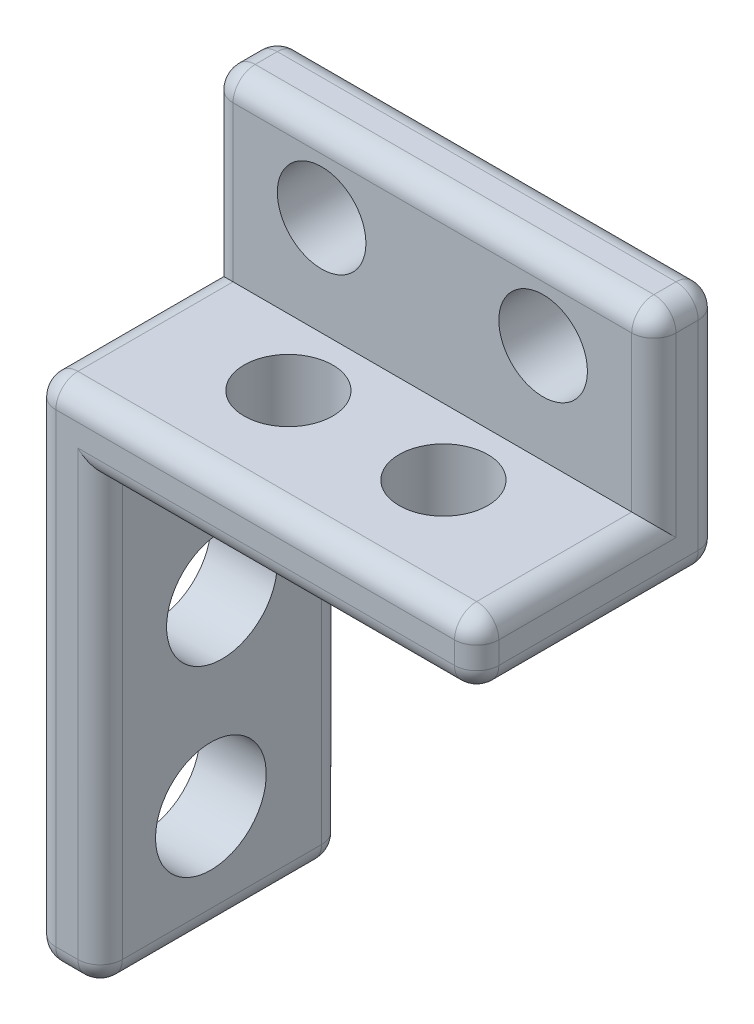
SolidWorks part; units mm, degrees
ref_plane "Front Plane" through (0, 0, 0) normal (0, 0, 1) x (1, 0, 0)
ref_plane "Top Plane" through (0, 0, 0) normal (0, 1, 0) x (1, 0, 0)
ref_plane "Right Plane" through (0, 0, 0) normal (1, 0, 0) x (0, 0, -1)
sketch "Sketch1" plane through (0, 0, 0) normal (1, 0, 0) x (0, 0, -1)
  line L1 (0, 0) -> (-3, 0)
  line L2 (0, 0) -> (0, 11)
  line L3 (0, 11) -> (-3, 11)
  line L4 (-3, 0) -> (-3, 11)
  line L5 (0, 0) -> (-11, 0)
  line L6 (0, 0) -> (0, 3)
  line L7 (0, 3) -> (-11, 3)
  line L8 (-11, 0) -> (-11, 3)
  dimension "D1" = 11
  dimension "D2" = 11
  dimension "D3" = 3
  dimension "D4" = 3
extrude "Boss-Extrude1" add sketch "Sketch1" along normal blind 20 contours L7 L2 L3 L4 | L2 L7 L4 L1 | L8 L5 L4 L7
sketch "Sketch2" plane through (0, 0, 3) normal (0, 0, 1) x (1, 0, 0)
  line L0 (20, 11) -> (0, 11) construction
  line L1 (20, 3) -> (20, 11) construction
  line L2 (0, 3) -> (0, 11) construction
  circle A0 centre (5, 7.5) radius 2
  circle A1 centre (15, 7.5) radius 2
  dimension "D1" = 4
  dimension "D2" = 4
  dimension "D4" = 3.5
  dimension "D5" = 4
  dimension "D6" = 5
  dimension "D7" = 5
  dimension "D3" = 3.5
extrude "Cut-Extrude1" cut sketch "Sketch2" against normal through all
sketch "Sketch3" plane through (0, 3, 0) normal (0, 1, 0) x (1, 0, 0)
  line L0 (20, -11) -> (0, -11) construction
  line L3 (20, -3) -> (20, -11) construction
  line L4 (0, -3) -> (0, -11) construction
  circle A0 centre (6.5, -6) radius 2
  circle A1 centre (13.5, -6) radius 2
  dimension "D1" = 4
  dimension "D2" = 4
  dimension "D3" = 4
  dimension "D4" = 5
  dimension "D5" = 5
  dimension "D6" = 7
  dimension "D7" = 6.5
  dimension "D8" = 6.5
extrude "Cut-Extrude2" cut sketch "Sketch3" against normal through all
sketch "Sketch4" plane through (0, 0, 0) normal (0, -1, 0) x (1, 0, 0)
  line L0 (20, 11) -> (0, 11) construction
  line L1 (0, 0) -> (3, 0)
  line L2 (0, 0) -> (0, 11)
  line L3 (0, 11) -> (3, 11)
  line L4 (3, 0) -> (3, 11)
  dimension "D1" = 3
extrude "Boss-Extrude2" add sketch "Sketch4" along normal blind 20
sketch "Sketch5" plane through (0, 0, 0) normal (-1, 0, 0) x (0, 0, 1)
  line L0 (11, -20) -> (0, -20) construction
  line L2 (11, -20) -> (11, 3) construction
  circle A0 centre (6, -15) radius 2.5
  dimension "D1" = 5
  dimension "D2" = 5
  dimension "D3" = 5
extrude "Cut-Extrude3" cut sketch "Sketch5" against normal through all
fillet "Fillet1" radius 1 22 edges at (3, -20, 5.5) (1.5, -20, 0) (0, -20, 5.5) (10, 3, 11) (11.5, 0, 11) (3, -10, 11) (1.5, -20, 11) (0, -8.5, 11) (20, 5.5, 0) (20, 0, 5.5) (20, 1.5, 11) (0, 3, 7) (20, 3, 7) (0, 7, 3) (20, 7, 3) (10, 11, 0) (0, 11, 1.5) (20, 11, 1.5) (10, 11, 3) (3, -10, 0) (11.5, 0, 0) (0, -4.5, 0)
sketch "Sketch6" plane through (3, 0, 0) normal (1, 0, 0) x (0, 0, -1)
  line L0 (-11, -19) -> (-11, 1) construction
  line L1 (-1, 0) -> (-10, 0) construction
  circle A0 centre (-5.5, -7) radius 2.5
  dimension "D1" = 5
  dimension "D2" = 5.5
  dimension "D3" = 7
extrude "Cut-Extrude4" cut sketch "Sketch6" against normal through all
